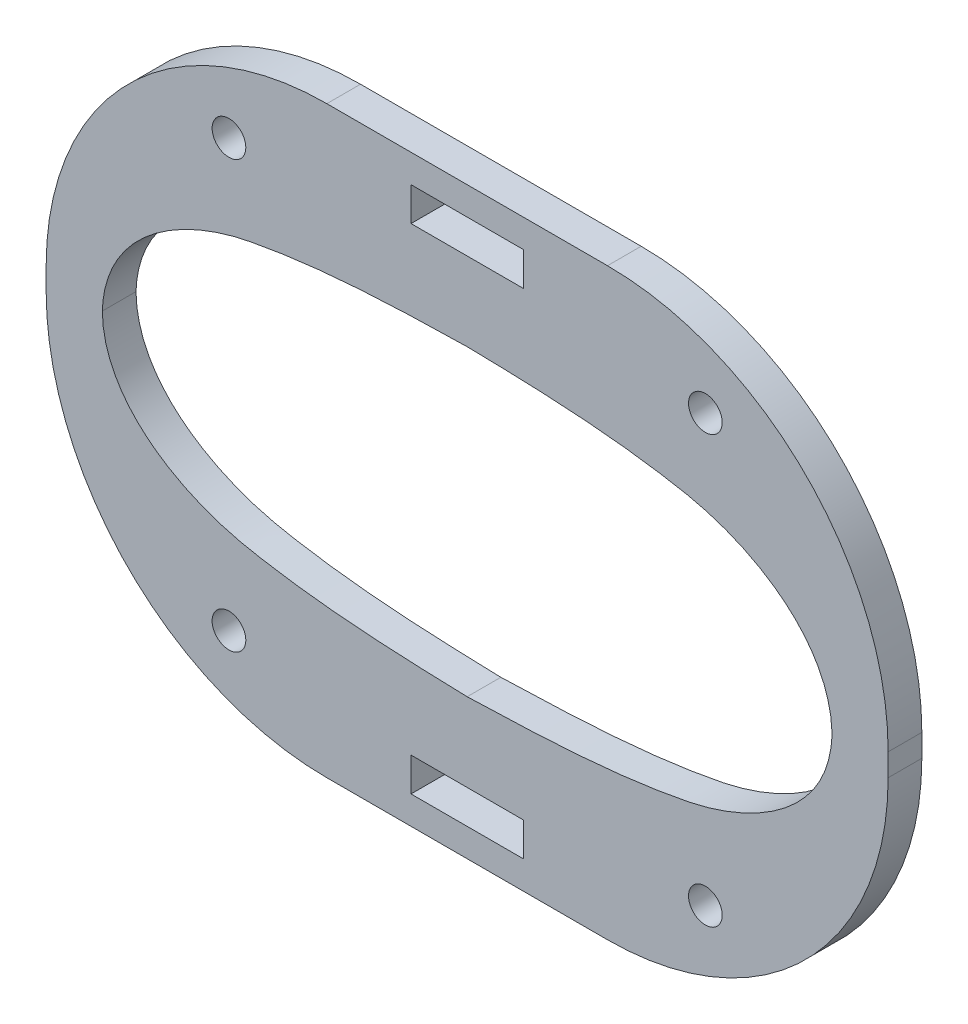
SolidWorks part; units mm, degrees
material "MDF"
ref_plane "Plano frontal" through (0, 0, 0) normal (0, 0, 1) x (1, 0, 0)
ref_plane "Plano superior" through (0, 0, 0) normal (0, 1, 0) x (1, 0, 0)
ref_plane "Plano direito" through (0, 0, 0) normal (1, 0, 0) x (0, 0, -1)
sketch "Esboço1" plane through (0, 0, 0) normal (0, 0, 1) x (1, 0, 0)
  line L0 (37.5, 0) -> (-37.5, 0) construction
  line L5 (12.5, 26) -> (-12.5, 26)
  line L6 (37.5, 1) -> (37.5, -1)
  line L7 (12.5, -26) -> (-12.5, -26)
  line L8 (-37.5, 1) -> (-37.5, -1)
  line L13 (37.5, 26) -> (-37.5, -26) construction
  line L14 (37.5, -26) -> (-37.5, 26) construction
  line L27 (0, -13.5) -> (0, 13.5) construction
  line L28 (32.5, 0) -> (-32.5, 0) construction
  line L29 (5, -23.5) -> (-5, -23.5)
  line L30 (5, -23.5) -> (5, -20.5)
  line L31 (5, -20.5) -> (-5, -20.5)
  line L32 (-5, -23.5) -> (-5, -20.5)
  line L33 (5, -23.5) -> (-5, -20.5) construction
  line L34 (5, -20.5) -> (-5, -23.5) construction
  line L35 (5, 20.5) -> (-5, 23.5) construction
  line L36 (5, 23.5) -> (-5, 20.5) construction
  line L37 (-5, 23.5) -> (-5, 20.5)
  line L38 (5, 20.5) -> (-5, 20.5)
  line L39 (5, 23.5) -> (5, 20.5)
  line L40 (5, 23.5) -> (-5, 23.5)
  line L42 (0, -26) -> (0, 26) construction
  arc A0 (-12.5, -26) -> (-37.5, -1) centre (-12.5, -1) cw
  arc A1 (-12.5, 26) -> (-37.5, 1) centre (-12.5, 1) ccw
  arc A2 (12.5, 26) -> (37.5, 1) centre (12.5, 1) cw
  arc A3 (37.5, -1) -> (12.5, -26) centre (12.5, -1) cw
  circle A4 centre (21.2178, -19) radius 1.5
  circle A5 centre (-21.2178, -19) radius 1.5
  circle A6 centre (21.2178, 19) radius 1.5
  circle A7 centre (-21.2178, 19) radius 1.5
  circle A8 centre (21.2178, -19) radius 5 construction
  spline S0 degree 3 poles (0, 13.5) (-6.5143, 13.3717) (-13.0616, 13.1595) (-25.8414, 10.6705) (-32.279, 6.557) (-32.5, 0) knots 0 0 0 0 0.5 0.5 1 1 1 1
  spline S1 degree 3 poles (32.5, 0) (32.4273, -6.5478) (25.8515, -10.5602) (13.0549, -13.0525) (6.5156, -13.3087) (0, -13.5) knots 0 0 0 0 0.5 0.5 1 1 1 1
  spline S2 degree 3 poles (0, 13.5) (6.5143, 13.3717) (13.0616, 13.1595) (25.8414, 10.6705) (32.279, 6.557) (32.5, 0) knots 0 0 0 0 0.5 0.5 1 1 1 1
  spline S3 degree 3 poles (-32.5, 0) (-32.4273, -6.5478) (-25.8515, -10.5602) (-13.0549, -13.0525) (-6.5156, -13.3087) (0, -13.5) knots 0 0 0 0 0.5 0.5 1 1 1 1
  point P0 (0, 0)
  point P1 (0, 0)
  point P6 (0, -22)
  point P18 (0, 22)
  point P45 (0, 0)
  dimension "D5" = 65
  dimension "D6" = 25
  dimension "D8" = 3
  dimension "D9" = 7
  dimension "D10" = 27
  dimension "D11" = 10
  dimension "D1" = 52
  dimension "D2" = 75
  dimension "D3" = 10
  dimension "D4" = 3
  dimension "D7" = 4
extrude "Ressalto-extrusão1" add sketch "Esboço1" along normal blind 3
